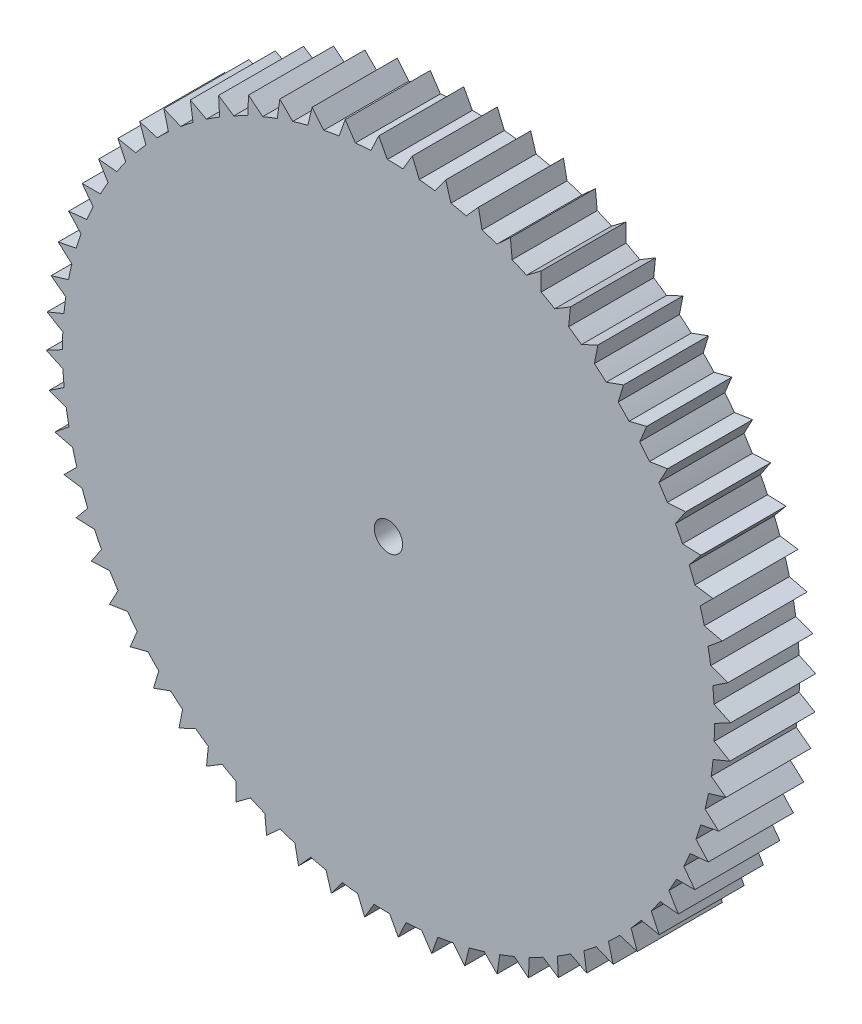
SolidWorks part; units mm, degrees
ref_plane "Front Plane" through (0, 0, 0) normal (0, 0, 1) x (1, 0, 0)
ref_plane "Top Plane" through (0, 0, 0) normal (0, 1, 0) x (1, 0, 0)
ref_plane "Right Plane" through (0, 0, 0) normal (1, 0, 0) x (0, 0, -1)
sketch "Sketch2" plane through (0, 0, 0) normal (0, 1, 0) x (1, 0, 0)
  line L1 (0, 19.1406) -> (0, 42.1406)
  line L2 (21.9625, 25.9706) -> (-21.9625, 25.9706)
  circle A0 centre (0, 19.1406) radius 23
  point P1 (0, 25.9706)
  point P7 (0, 25.9706)
  dimension "D1" = 16.17
  dimension "D2" = 46
ref_plane "Plane1" through (0, 0, -25.9706) normal (0, 0, -1) x (-1, 0, 0)
sketch "Sketch3" plane through (0, 0, -25.9706) normal (0, 0, -1) x (-1, 0, 0)
  line L0 (21.9625, 0) -> (-21.9625, 0)
  line L1 (21.9625, 0) -> (21.9625, 85)
  line L2 (-21.9625, 0) -> (-21.9625, 85)
  line L3 (21.9625, 85) -> (-21.9625, 85)
  line L4 (21.9625, 0) -> (-21.9625, 85) construction
  line L5 (-21.9625, 0) -> (21.9625, 85) construction
  line L9 (34.4493, 57.3155) -> (18.9158, 10.4622)
  line L10 (32.1526, 56.3278) -> (13.3127, 12.5933)
  line L11 (-26.4622, 69.0707) -> (-24.6744, 67.3228)
  line L12 (0, 0) -> (0, 85)
  arc A0 (-24.6744, 67.3228) -> (32.1526, 56.3278) centre (0, 42.5) cw
  arc A1 (23.9765, 17.0024) -> (8.6581, 8.5878) centre (0, 42.5) cw
  arc A2 (-26.4622, 69.0707) -> (34.4493, 57.3155) centre (0, 42.5) cw
  circle A3 centre (16.0681, 11.4063) radius 2
  arc A4 (13.3127, 12.5933) -> (18.9158, 10.4622) centre (16.0681, 11.4063) ccw
  circle A5 centre (0, 42.5) radius 33.5
  circle A6 centre (0, 64.2) radius 11.5
  point P6 (0, 42.5)
  point P10 (16.0681, 11.4063)
  point P13 (-21.9625, 69.7516)
  point P23 (0, 42.5)
  point P26 (0, 76)
  point P27 (0, 75.7)
  point P28 (0.2784, 75.6966)
  point P29 (-1.5967, 75.5886)
  point P30 (0, 0)
  point P31 (0, 71.5)
  point P35 (0, 0)
  dimension "D2" = 5.8944
  dimension "D4" = 0.3
  dimension "D5" = 67
  dimension "D6" = 23
  dimension "D1" = 85
  dimension "D3" = 15.2484
  dimension "D7" = 7.3
extrude "Boss-Extrude1" add sketch "Sketch3" along normal blind 3
sketch "Sketch7" plane through (0, 0, -28.9706) normal (0, 0, -1) x (-1, 0, 0)
  circle A0 centre (0, 64.2) radius 2
extrude "Boss-Extrude4" add sketch "Sketch7" along normal blind 3
sketch "Sketch8" plane through (0, 0, -31.9706) normal (0, 0, -1) x (-1, 0, 0)
  line L0 (0.4, 62.4) -> (-0.4, 62.4)
  line L2 (-0.4, 62.4) -> (0, 61.6)
  line L3 (0, 0) -> (0, 85) construction
  line L4 (0, 61.6) -> (0.4, 62.4)
  point P0 (0, 0)
  point P3 (0, 62.4)
  dimension "D1" = 1.8
  dimension "D2" = 0.8
  dimension "D3" = 0.8
extrude "Boss-Extrude5" add sketch "Sketch8" against normal blind 3
pattern_circular "CirPattern2" count 20 over 360 about axis through (0, 64.1682, 0) along (0, 0, 1) of "Boss-Extrude5"
sketch "Sketch9" plane through (0, 0, -31.9706) normal (0, 0, -1) x (-1, 0, 0)
  circle A0 centre (0, 64.2) radius 0.5
extrude "Cut-Extrude1" cut sketch "Sketch9" against normal blind 6
sketch "Sketch10" plane through (0, 0, -25.9706) normal (0, 0, 1) x (1, 0, 0)
  line L0 (0, 75.7) -> (1.5967, 75.5886)
  line L1 (0.7984, 75.6443) -> (0, 64.2)
  line L2 (0.3844, 75.4754) -> (1.1844, 75.4132)
  line L3 (1.1844, 75.4132) -> (0.8402, 76.2443)
  line L4 (0.8402, 76.2443) -> (0.3844, 75.4754)
  line L5 (0.8402, 76.2443) -> (0.7984, 75.6443)
  point P10 (0.7844, 75.4443)
  circle M5 centre (0, 64.2) radius 11.5
  dimension "D1" = 0.8
  dimension "D2" = 0.8
  dimension "D3" = 0.2
extrude "Boss-Extrude6" add sketch "Sketch10" against normal blind 3 contours L5 L4 M5 | L3 L5 M5
pattern_circular "CirPattern3" count 64 over 360 about axis through (0, 64.2, 0) along (0, 0, 1) of "Boss-Extrude6"
